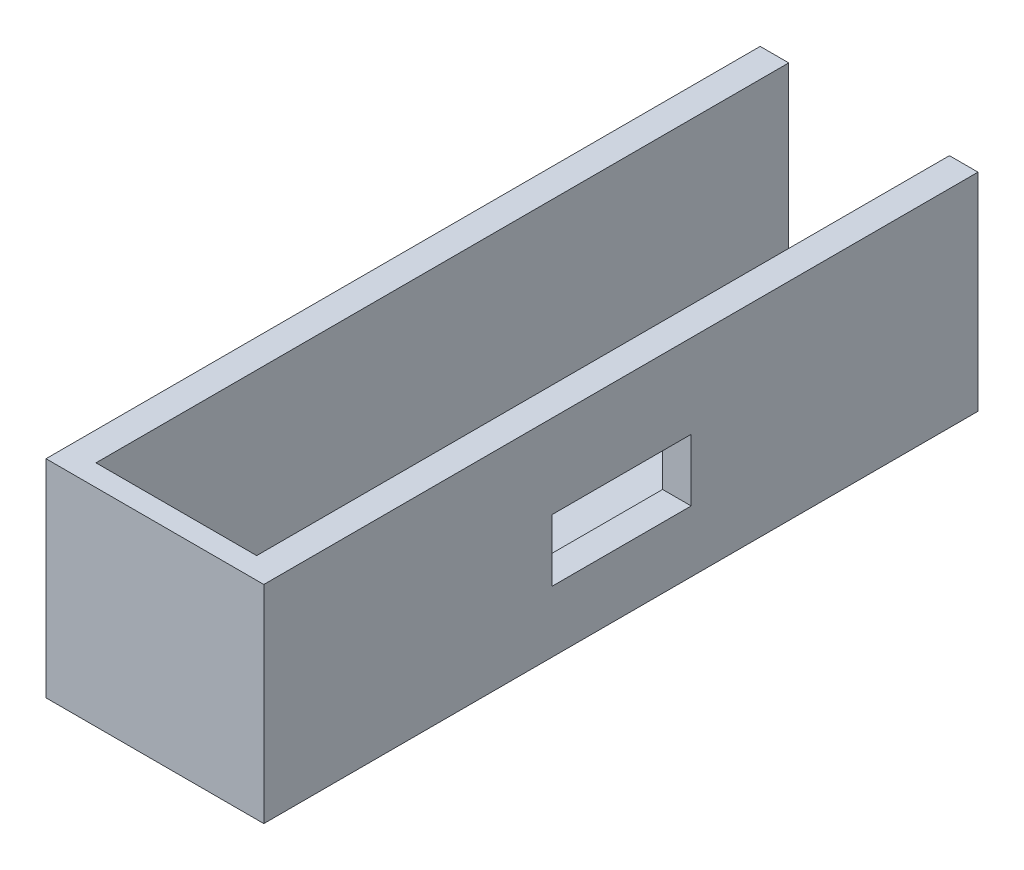
SolidWorks part; units mm, degrees
ref_plane "Front Plane" through (0, 0, 0) normal (0, 0, 1) x (1, 0, 0)
ref_plane "Top Plane" through (0, 0, 0) normal (0, 1, 0) x (1, 0, 0)
ref_plane "Right Plane" through (0, 0, 0) normal (1, 0, 0) x (0, 0, -1)
sketch "Sketch1" plane through (0, 0, 0) normal (0, 0, 1) x (1, 0, 0)
  line L0 (-9.8486, 0) -> (-9.8486, -25)
  line L1 (-9.8486, -25) -> (12.6514, -25)
  line L2 (12.6514, -25) -> (12.6514, 0)
  line L3 (12.6514, 0) -> (16.6514, 0)
  line L4 (16.6514, 0) -> (16.6514, -29)
  line L5 (16.6514, -29) -> (-13.8486, -29)
  line L6 (-13.8486, -29) -> (-13.8486, 0)
  line L7 (-13.8486, 0) -> (-9.8486, 0)
  dimension "D1" = 30.5
  dimension "D2" = 4
  dimension "D3" = 4
  dimension "D4" = 25
extrude "Boss-Extrude1" add sketch "Sketch1" along normal mid plane 100
sketch "Sketch2" plane through (0, 0, 50) normal (0, 0, 1) x (1, 0, 0)
  line L1 (-13.8486, 0) -> (16.6514, 0)
  line L2 (-13.8486, 0) -> (-13.8486, -29)
  line L3 (-13.8486, -29) -> (16.6514, -29)
  line L4 (16.6514, 0) -> (16.6514, -29)
extrude "Boss-Extrude2" add sketch "Sketch2" against normal blind 3
sketch "Sketch3" plane through (0, 0, 0) normal (1, 0, 0) x (0, 0, -1)
  line L1 (-9.6612, -20.398) -> (9.8388, -20.398)
  line L2 (-9.6612, -20.398) -> (-9.6612, -11.708)
  line L3 (-9.6612, -11.708) -> (9.8388, -11.708)
  line L4 (9.8388, -20.398) -> (9.8388, -11.708)
  line L5 (-9.6612, -20.398) -> (9.8388, -11.708) construction
  line L6 (-9.6612, -11.708) -> (9.8388, -20.398) construction
  point P0 (0.0888, -16.053)
  dimension "D1" = 19.5
  dimension "D2" = 8.69
extrude "Cut-Extrude1" cut sketch "Sketch3" along normal blind 30
